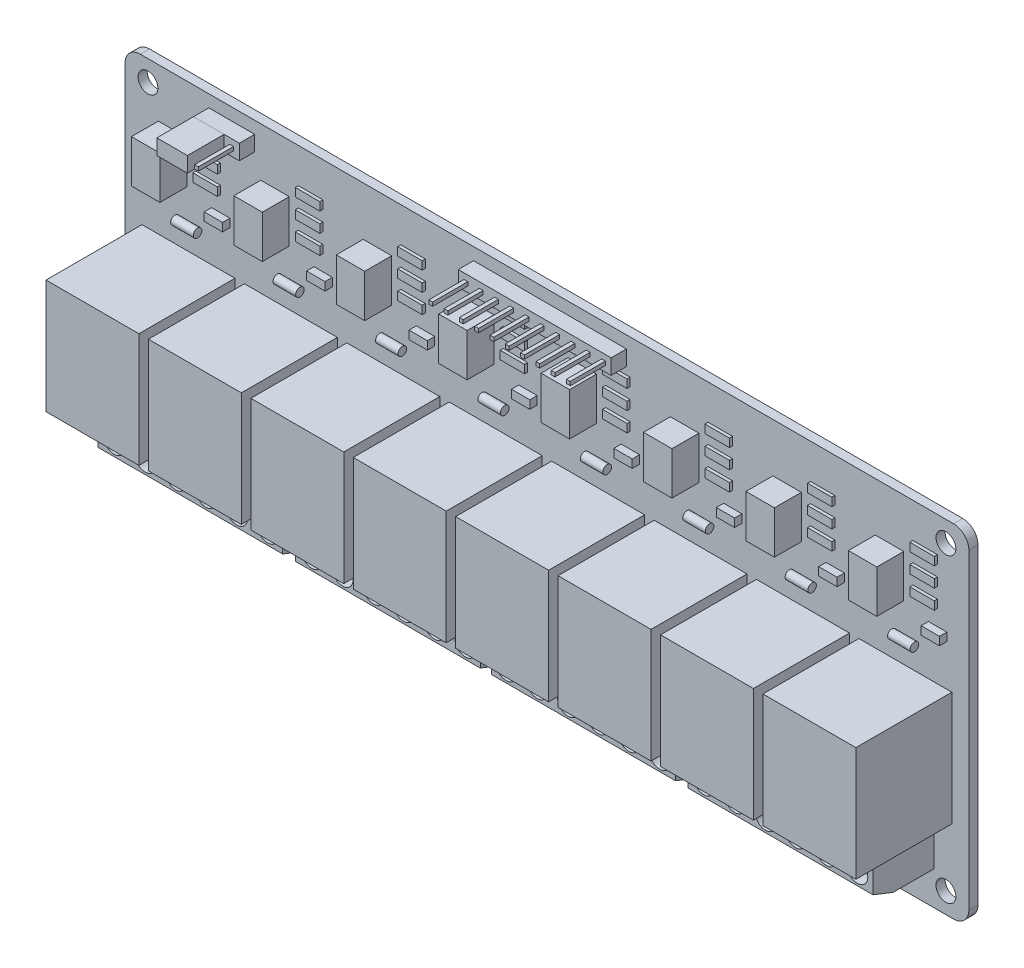
SolidWorks part; units mm, degrees
ref_plane "Front Plane" through (0, 0, 0) normal (0, 0, 1) x (1, 0, 0)
ref_plane "Top Plane" through (0, 0, 0) normal (0, 1, 0) x (1, 0, 0)
ref_plane "Right Plane" through (0, 0, 0) normal (1, 0, 0) x (0, 0, -1)
sketch "Sketch1" plane through (0, 0, 0) normal (0, 0, 1) x (1, 0, 0)
  line L0 (0, 0) -> (0, -24.625) construction
  line L1 (69, -28) -> (-69, -28)
  line L2 (69, -28) -> (69, 28)
  line L3 (69, 28) -> (-69, 28)
  line L4 (-69, -28) -> (-69, 28)
  line L5 (69, -28) -> (-69, 28) construction
  line L6 (69, 28) -> (-69, -28) construction
  line L7 (0, -24.625) -> (-65.25, -24.625) construction
  line L8 (-65.25, -24.625) -> (-65.25, 24.625) construction
  line L9 (-65.25, 24.625) -> (0, 24.625) construction
  line L10 (0, 24.625) -> (65.25, 24.625) construction
  line L11 (65.25, 24.625) -> (65.25, -24.625) construction
  line L12 (65.25, -24.625) -> (0, -24.625) construction
  line L13 (0, 24.625) -> (0, 0) construction
  circle A0 centre (-65.25, 24.625) radius 1.625
  circle A1 centre (-65.25, -24.625) radius 1.625
  circle A2 centre (65.25, -24.625) radius 1.625
  circle A3 centre (65.25, 24.625) radius 1.625
  point P0 (0, 0)
  dimension "D3" = 3.25
  dimension "D4" = 52.5
  dimension "D5" = 133.75
  dimension "D1" = 56
  dimension "D2" = 138
extrude "Boss-Extrude1" add sketch "Sketch1" along normal blind 1.5
fillet "Fillet1" radius 2.5 4 edges at (69, -28, 0.75) (69, 28, 0.75) (-69, -28, 0.75) (-69, 28, 0.75)
sketch "Sketch2" plane through (0, 0, 1.5) normal (0, 0, 1) x (1, 0, 0)
  line L0 (66.5, 28) -> (-66.5, 28) construction
  line L1 (66.225, -14.65) -> (51.025, -14.65)
  line L2 (66.225, -14.65) -> (66.225, 4)
  line L3 (66.225, 4) -> (51.025, 4)
  line L4 (51.025, -14.65) -> (51.025, 4)
  line L5 (66.225, -14.65) -> (51.025, 4) construction
  line L6 (66.225, 4) -> (51.025, -14.65) construction
  line L7 (69, -25.5) -> (69, 25.5) construction
  point P0 (58.625, -5.325)
  dimension "D1" = 15.2
  dimension "D2" = 18.65
  dimension "D3" = 24
  dimension "D4" = 2.775
extrude "Boss-Extrude2" add sketch "Sketch2" along normal blind 15.7
sketch "Sketch3" plane through (0, 0, 1.5) normal (0, 0, 1) x (1, 0, 0)
  line L0 (69, -25.5) -> (69, 25.5) construction
  line L1 (58.35, 13) -> (53.7, 13)
  line L2 (58.35, 13) -> (58.35, 20)
  line L3 (58.35, 20) -> (53.7, 20)
  line L4 (53.7, 13) -> (53.7, 20)
  line L5 (58.35, 13) -> (53.7, 20) construction
  line L6 (58.35, 20) -> (53.7, 13) construction
  line L7 (66.5, 28) -> (-66.5, 28) construction
  point P0 (56.025, 16.5)
  dimension "D1" = 7
  dimension "D2" = 4.65
  dimension "D3" = 10.65
  dimension "D4" = 8
extrude "Boss-Extrude3" add sketch "Sketch3" along normal blind 4.4
sketch "Sketch4" plane through (69, 0, 0) normal (1, 0, 0) x (0, 0, -1)
  line L0 (-1.5, -25.5) -> (-1.5, 25.5) construction
  line L1 (0, 28) -> (-1.5, 28) construction
  circle A0 centre (-2.19, 8.05) radius 0.7
  point P5 (-0.75, 28)
  dimension "D2" = 1.4
  dimension "D1" = 19.95
  dimension "D3" = 0.69
extrude "Boss-Extrude4" add sketch "Sketch4" against normal blind 3.7 from offset 8.2 offset against normal yes
sketch "Sketch5" plane through (0, 0, 1.5) normal (0, 0, 1) x (1, 0, 0)
  line L0 (69, -25.5) -> (69, 25.5) construction
  line L1 (65.4, 10.75) -> (62.4, 10.75)
  line L2 (65.4, 10.75) -> (65.4, 12.1)
  line L3 (65.4, 12.1) -> (62.4, 12.1)
  line L4 (62.4, 10.75) -> (62.4, 12.1)
  line L5 (65.4, 10.75) -> (62.4, 12.1) construction
  line L6 (65.4, 12.1) -> (62.4, 10.75) construction
  line L7 (66.225, 4) -> (51.025, 4) construction
  point P0 (63.9, 11.425)
  dimension "D1" = 1.35
  dimension "D2" = 3
  dimension "D3" = 3.6
  dimension "D4" = 6.75
extrude "Boss-Extrude5" add sketch "Sketch5" along normal blind 1.2
sketch "Sketch6" plane through (0, 0, 1.5) normal (0, 0, 1) x (1, 0, 0)
  line L0 (61.85, 20.95) -> (61.85, 19.15) construction
  line L1 (63.85, 16) -> (59.85, 16)
  line L2 (63.85, 16) -> (63.85, 14.65)
  line L3 (63.85, 14.65) -> (59.85, 14.65)
  line L4 (59.85, 16) -> (59.85, 14.65)
  line L5 (63.85, 16) -> (59.85, 14.65) construction
  line L6 (63.85, 14.65) -> (59.85, 16) construction
  line L7 (63.85, 19.15) -> (59.85, 19.15)
  line L8 (63.85, 19.15) -> (63.85, 17.8)
  line L9 (63.85, 17.8) -> (59.85, 17.8)
  line L10 (59.85, 19.15) -> (59.85, 17.8)
  line L11 (63.85, 19.15) -> (59.85, 17.8) construction
  line L12 (63.85, 17.8) -> (59.85, 19.15) construction
  line L13 (63.85, 22.3) -> (59.85, 22.3)
  line L14 (63.85, 22.3) -> (63.85, 20.95)
  line L15 (63.85, 20.95) -> (59.85, 20.95)
  line L16 (59.85, 22.3) -> (59.85, 20.95)
  line L17 (63.85, 22.3) -> (59.85, 20.95) construction
  line L18 (63.85, 20.95) -> (59.85, 22.3) construction
  line L19 (61.85, 17.8) -> (61.85, 16) construction
  line L20 (69, -25.5) -> (69, 25.5) construction
  line L21 (66.5, 28) -> (-66.5, 28) construction
  point P0 (61.85, 15.325)
  point P5 (61.85, 18.475)
  point P10 (61.85, 21.625)
  dimension "D1" = 1.35
  dimension "D2" = 4
  dimension "D3" = 1.8
  dimension "D4" = 5.15
  dimension "D5" = 5.7
extrude "Boss-Extrude6" add sketch "Sketch6" along normal blind 0.5
pattern_linear "LPattern1" count 8 spacing 16.75 along (-1, 0, 0) of "Boss-Extrude2", "Boss-Extrude3", "Boss-Extrude4", "Boss-Extrude5", "Boss-Extrude6"
sketch "Sketch7" plane through (69, 0, 0) normal (1, 0, 0) x (0, 0, -1)
  line L0 (-1.5, -15.45) -> (-8.2, -15.45)
  line L1 (-1.5, -25.5) -> (-1.5, 25.5) construction
  line L2 (-8.2, -15.45) -> (-11.5, -17.05)
  line L3 (-11.5, -17.05) -> (-11.5, -21.15)
  line L4 (-11.5, -21.15) -> (-8.2, -22.45)
  line L5 (-8.2, -22.45) -> (-1.5, -22.45)
  line L6 (-1.5, -22.45) -> (-1.5, -15.45)
  line L7 (-17.2, -14.65) -> (-1.5, -14.65) construction
  dimension "D1" = 10
  dimension "D2" = 0.8
  dimension "D3" = 7.8
  dimension "D4" = 3.3
  dimension "D5" = 1.6
  dimension "D6" = 1.3
extrude "Boss-Extrude7" add sketch "Sketch7" against normal blind 126.75 from offset 5.675 offset against normal yes
sketch "Sketch8" plane through (0, -22.45, 0) normal (0, -1, 0) x (1, 0, 0)
  line L0 (-0.9, 11.5) -> (-0.9, 1.5)
  line L1 (-63.425, 1.5) -> (63.325, 1.5) construction
  line L3 (-0.9, 1.5) -> (0.9, 1.5)
  line L4 (0.9, 1.5) -> (0.9, 11.5)
  line L5 (0.9, 11.5) -> (-0.9, 11.5)
  line L6 (0, 1.5) -> (0, 0) construction
  line L7 (-63.425, 11.5) -> (63.325, 11.5) construction
  line L8 (-66.5, 1.5) -> (66.5, 1.5) construction
  line L9 (-33.2125, 11.5) -> (-31.1125, 11.5)
  line L10 (-33.2125, 11.5) -> (-33.2125, 1.5)
  line L11 (-33.2125, 1.5) -> (-31.1125, 1.5)
  line L12 (-31.1125, 11.5) -> (-31.1125, 1.5)
  line L13 (-63.425, 8.2) -> (-33.2125, 8.2) construction
  line L14 (33.1125, 11.5) -> (31.0125, 11.5)
  line L15 (33.1125, 11.5) -> (33.1125, 1.5)
  line L16 (33.1125, 1.5) -> (31.0125, 1.5)
  line L17 (31.0125, 11.5) -> (31.0125, 1.5)
  line L18 (-63.425, 8.2) -> (63.325, 8.2) construction
  line L19 (-0.9, 8.2) -> (-31.1125, 8.2) construction
  line L20 (63.325, 8.2) -> (33.1125, 8.2) construction
  dimension "D1" = 1.8
  dimension "D2" = 2.1
extrude "Cut-Extrude1" cut sketch "Sketch8" against normal up to surface (7 mm away) up to face at (-0.05, -15.45, 4.85)
sketch "Sketch9" plane through (0, 0, 11.5) normal (0, 0, 1) x (1, 0, 0)
  line L0 (60.775, -19.1) -> (62.475, -19.1) construction
  line L1 (62.475, -19.1) -> (63.325, -19.1) construction
  line L2 (63.325, -17.05) -> (63.325, -21.15) construction
  line L3 (60.775, -19.1) -> (59.075, -19.1) construction
  line L4 (59.075, -19.1) -> (57.425, -19.1) construction
  line L5 (57.425, -19.1) -> (54.025, -19.1) construction
  line L6 (54.025, -19.1) -> (52.375, -19.1) construction
  line L7 (45.7625, -19.1) -> (44.0625, -19.1) construction
  line L8 (44.0625, -19.1) -> (42.4125, -19.1) construction
  line L9 (42.4125, -19.1) -> (39.0125, -19.1) construction
  line L10 (39.0125, -19.1) -> (37.3625, -19.1) construction
  line L11 (37.3625, -19.1) -> (33.9625, -19.1) construction
  line L12 (33.9625, -19.1) -> (33.1125, -19.1) construction
  line L13 (33.1125, -17.05) -> (33.1125, -21.15) construction
  circle A0 centre (60.775, -19.1) radius 1.7
  circle A1 centre (55.725, -19.1) radius 1.7
  circle A2 centre (50.675, -19.1) radius 1.7
  circle A3 centre (45.7625, -19.1) radius 1.7
  circle A4 centre (40.7125, -19.1) radius 1.7
  circle A5 centre (35.6625, -19.1) radius 1.7
  dimension "D1" = 3.4
  dimension "D2" = 0.85
  dimension "D3" = 1.65
extrude "Cut-Extrude2" cut sketch "Sketch9" against normal blind 2
ref_plane "Plane1" through (32.0625, 0, 0) normal (1, 0, 0) x (0, 0, -1)
mirror "Mirror1" about plane through (32.0625, 0, 0) normal (1, 0, 0) of "Cut-Extrude2"
mirror "Mirror2" about plane through (0, 0, 0) normal (1, 0, 0) of "Mirror1", "Cut-Extrude2"
sketch "Sketch11" plane through (0, 0, 1.5) normal (0, 0, 1) x (1, 0, 0)
  line L0 (66.5, 28) -> (-66.5, 28) construction
  line L1 (-52.8, 23.5) -> (-55.3, 23.5)
  line L2 (-52.8, 23.5) -> (-52.8, 26)
  line L3 (-52.8, 26) -> (-55.3, 26)
  line L4 (-55.3, 23.5) -> (-55.3, 26)
  line L5 (-52.8, 23.5) -> (-55.3, 26) construction
  line L6 (-52.8, 26) -> (-55.3, 23.5) construction
  line L7 (-69, 25.5) -> (-69, -25.5) construction
  point P0 (-54.05, 24.75)
  dimension "D1" = 2
  dimension "D2" = 13.7
  dimension "D3" = 2.5
extrude "Boss-Extrude9" add sketch "Sketch11" along normal blind 2.5
sketch "Sketch12" plane through (0, 0, 4) normal (0, 0, 1) x (1, 0, 0)
  line L0 (-55.3, 26) -> (-52.8, 23.5) construction
  line L1 (-53.74, 24.44) -> (-54.36, 24.44)
  line L2 (-53.74, 24.44) -> (-53.74, 25.06)
  line L3 (-53.74, 25.06) -> (-54.36, 25.06)
  line L4 (-54.36, 24.44) -> (-54.36, 25.06)
  line L5 (-53.74, 24.44) -> (-54.36, 25.06) construction
  line L6 (-53.74, 25.06) -> (-54.36, 24.44) construction
  point P0 (-54.05, 24.75)
  dimension "D1" = 0.62
extrude "Boss-Extrude10" add sketch "Sketch12" along normal blind 5.75
pattern_linear "LPattern2" count 3 spacing 2.5 along (1, 0, 0) of "Boss-Extrude9", "Boss-Extrude10"
sketch "Sketch13" plane through (0, 0, 4) normal (0, 0, 1) x (1, 0, 0)
  line L0 (-55.3, 23.5) -> (-47.8, 23.5) construction
  line L1 (-55.3, 26) -> (-50.3, 26)
  line L2 (-55.3, 26) -> (-55.3, 23.5)
  line L3 (-55.3, 23.5) -> (-50.3, 23.5)
  line L4 (-50.3, 26) -> (-50.3, 23.5)
  line L5 (-51.24, 24.75) -> (-50.3, 24.75) construction
  line L6 (-51.24, 24.44) -> (-51.24, 25.06) construction
  line L7 (-50.3, 24.75) -> (-49.36, 24.75) construction
  line L8 (-49.36, 25.06) -> (-49.36, 24.44) construction
extrude "Boss-Extrude11" add sketch "Sketch13" along normal blind 6 separate body
sketch "Sketch15" plane through (0, 0, 1.5) normal (0, 0, 1) x (1, 0, 0)
  line L0 (69, -25.5) -> (69, 25.5) construction
  line L1 (13, 23.5) -> (10.5, 23.5)
  line L2 (13, 23.5) -> (13, 26)
  line L3 (13, 26) -> (10.5, 26)
  line L4 (10.5, 23.5) -> (10.5, 26)
  line L5 (13, 23.5) -> (10.5, 26) construction
  line L6 (13, 26) -> (10.5, 23.5) construction
  line L7 (-47.8, 23.5) -> (-47.8, 26) construction
  line L8 (-47.8, 26) -> (-55.3, 26) construction
  point P0 (11.75, 24.75)
  dimension "D1" = 56
extrude "Boss-Extrude12" add sketch "Sketch15" along normal up to surface (2.5 mm away) up to face at (-51.55, 24.75, 4)
sketch "Sketch16" plane through (0, 0, 4) normal (0, 0, 1) x (1, 0, 0)
  line L0 (10.5, 26) -> (13, 23.5) construction
  line L1 (12.06, 24.44) -> (11.44, 24.44)
  line L2 (12.06, 24.44) -> (12.06, 25.06)
  line L3 (12.06, 25.06) -> (11.44, 25.06)
  line L4 (11.44, 24.44) -> (11.44, 25.06)
  line L5 (12.06, 24.44) -> (11.44, 25.06) construction
  line L6 (12.06, 25.06) -> (11.44, 24.44) construction
  line L7 (-49.36, 24.44) -> (-48.74, 24.44) construction
  point P0 (11.75, 24.75)
extrude "Boss-Extrude13" add sketch "Sketch16" along normal blind 5.75
pattern_linear "LPattern5" count 10 spacing 2.5 along (-1, 0, 0) of "Boss-Extrude12", "Boss-Extrude13"
